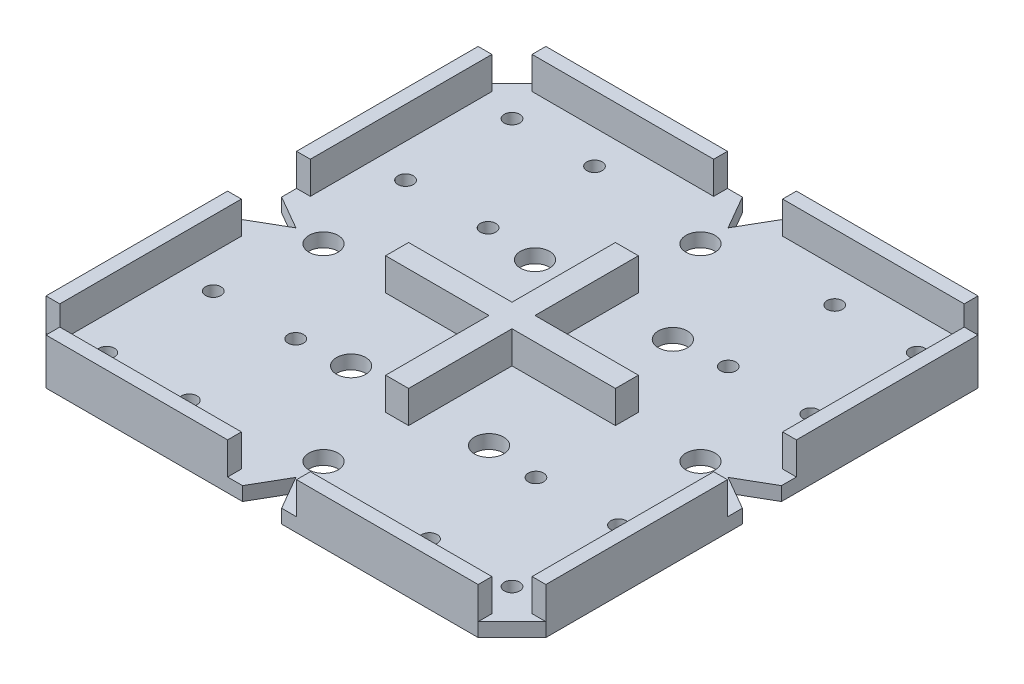
SolidWorks part; units mm, degrees
ref_plane "Front Plane" through (0, 0, 0) normal (0, 0, 1) x (1, 0, 0)
ref_plane "Top Plane" through (0, 0, 0) normal (0, 1, 0) x (1, 0, 0)
ref_plane "Right Plane" through (0, 0, 0) normal (1, 0, 0) x (0, 0, -1)
sketch "Sketch1" plane through (0, 0, 0) normal (0, 1, 0) x (1, 0, 0)
  line L1 (0, 0) -> (120, 0)
  line L2 (0, 0) -> (0, 120)
  line L3 (0, 120) -> (120, 120)
  line L4 (120, 0) -> (120, 120)
  dimension "D1" = 120
extrude "Boss-Extrude1" add sketch "Sketch1" along normal blind 3
sketch "Sketch3" plane through (0, 3, 0) normal (0, 1, 0) x (1, 0, 0)
  line L0 (0, 0) -> (120, 0) construction
  line L1 (0, 120) -> (0, 0) construction
  line L2 (0, 60) -> (120, 60) construction
  line L3 (120, 0) -> (120, 120) construction
  line L4 (60, 0) -> (60, 120) construction
  line L5 (120, 120) -> (0, 120) construction
  circle A0 centre (15.92, 15.92) radius 1.675
  circle A1 centre (33.87, 15.92) radius 1.675
  circle A2 centre (15.92, 39.08) radius 1.675
  circle A3 centre (33.87, 39.08) radius 1.675
  circle A4 centre (33.87, 80.92) radius 1.675
  circle A5 centre (15.92, 80.92) radius 1.675
  circle A6 centre (33.87, 104.08) radius 1.675
  circle A7 centre (15.92, 104.08) radius 1.675
  circle A8 centre (86.13, 39.08) radius 1.675
  circle A9 centre (104.08, 39.08) radius 1.675
  circle A10 centre (86.13, 15.92) radius 1.675
  circle A11 centre (104.08, 15.92) radius 1.675
  circle A12 centre (104.08, 104.08) radius 1.675
  circle A13 centre (86.13, 104.08) radius 1.675
  circle A14 centre (104.08, 80.92) radius 1.675
  circle A15 centre (86.13, 80.92) radius 1.675
  dimension "D5" = 3.35
  dimension "D1" = 15.92
  dimension "D2" = 15.92
  dimension "D3" = 17.95
  dimension "D4" = 23.16
extrude "Cut-Extrude2" cut sketch "Sketch3" against normal through all
sketch "Sketch4" plane through (0, 3, 0) normal (0, 1, 0) x (1, 0, 0)
  line L0 (52.5, 120) -> (60, 107.0096)
  line L1 (120, 120) -> (0, 120) construction
  line L2 (60, 107.0096) -> (67.5, 120)
  line L3 (67.5, 120) -> (52.5, 120)
  line L4 (0, 67.5) -> (12.9904, 60)
  line L5 (0, 120) -> (0, 0) construction
  line L6 (12.9904, 60) -> (0, 52.5)
  line L7 (0, 52.5) -> (0, 67.5)
  line L8 (120, 67.5) -> (107.0096, 60)
  line L9 (120, 0) -> (120, 120) construction
  line L10 (107.0096, 60) -> (120, 52.5)
  line L11 (120, 52.5) -> (120, 67.5)
  line L12 (67.5, 0) -> (60, 12.9904)
  line L13 (0, 0) -> (120, 0) construction
  line L14 (60, 12.9904) -> (52.5, 0)
  line L15 (52.5, 0) -> (67.5, 0)
  line L16 (0, 52.5) -> (0, 0) construction
  line L17 (0, 67.5) -> (0, 120) construction
  line L18 (52.5, 120) -> (0, 120) construction
  line L19 (67.5, 120) -> (120, 120) construction
  line L20 (120, 67.5) -> (120, 120) construction
  line L21 (120, 52.5) -> (120, 0) construction
  line L22 (120, 0) -> (67.5, 0) construction
  line L23 (52.5, 0) -> (0, 0) construction
  dimension "D1" = 15
  dimension "D2" = 15
extrude "Cut-Extrude3" cut sketch "Sketch4" against normal through all
sketch "Sketch5" plane through (0, 3, 0) normal (0, 1, 0) x (1, 0, 0)
  line L0 (60, 12.9904) -> (60, 107.0096) construction
  line L1 (12.9904, 60) -> (107.0096, 60) construction
  circle A0 centre (75, 40) radius 3.175
  circle A1 centre (45, 40) radius 3.175
  circle A2 centre (45, 80) radius 3.175
  circle A3 centre (75, 80) radius 3.175
  circle A8 centre (101.0096, 60) radius 3.175
  circle A9 centre (60, 18.9904) radius 3.175
  circle A10 centre (60, 101.0096) radius 3.175
  circle A11 centre (18.9904, 60) radius 3.175
  point P28 (0, 0)
  dimension "D3" = 6.35
  dimension "D1" = 20
  dimension "D2" = 15
  dimension "D4" = 6
  dimension "D5" = 6
  dimension "D6" = 6
  dimension "D7" = 6
extrude "Cut-Extrude4" cut sketch "Sketch5" against normal up to surface (3 mm away) up to face at (60, 0, -60)
sketch "Sketch8" plane through (0, 3, 0) normal (0, 1, 0) x (1, 0, 0)
  line L0 (60, 107.0096) -> (60, 85) construction
  line L1 (60, 12.9904) -> (60, 35) construction
  line L2 (12.9904, 60) -> (35, 60) construction
  line L3 (62.5, 85) -> (57.5, 85)
  line L4 (62.5, 85) -> (62.5, 35)
  line L5 (62.5, 35) -> (57.5, 35)
  line L6 (57.5, 85) -> (57.5, 35)
  line L7 (107.0096, 60) -> (85, 60) construction
  line L8 (104.08, 105.755) -> (87.805, 105.755) construction
  line L9 (85, 62.5) -> (35, 62.5)
  line L10 (85, 62.5) -> (85, 57.5)
  line L11 (85, 57.5) -> (35, 57.5)
  line L12 (35, 62.5) -> (35, 57.5)
  line L13 (107.0096, 114.3775) -> (67.5, 114.3775)
  line L14 (107.0096, 114.3775) -> (107.0096, 111.3775)
  line L15 (107.0096, 111.3775) -> (67.5, 111.3775)
  line L16 (67.5, 114.3775) -> (67.5, 111.3775)
  line L17 (107.0096, 105.755) -> (107.0096, 111.3775) construction
  line L18 (107.0096, 114.3775) -> (107.0096, 120) construction
  line L19 (120, 120) -> (67.5, 120) construction
  line L20 (105.755, 104.3139) -> (105.755, 72.5955) construction
  line L21 (111.3775, 107.0096) -> (105.755, 107.0096) construction
  line L22 (114.3775, 107.0096) -> (111.3775, 107.0096)
  line L23 (114.3775, 107.0096) -> (114.3775, 67.5)
  line L24 (114.3775, 67.5) -> (111.3775, 67.5)
  line L25 (111.3775, 107.0096) -> (111.3775, 67.5)
  line L26 (114.3775, 107.0096) -> (120, 107.0096) construction
  line L27 (120, 67.5) -> (120, 120) construction
  line L28 (114.3775, 52.5) -> (111.3775, 52.5)
  line L29 (111.3775, 12.9904) -> (111.3775, 52.5)
  line L30 (114.3775, 12.9904) -> (111.3775, 12.9904)
  line L31 (114.3775, 12.9904) -> (114.3775, 52.5)
  line L32 (107.0096, 8.6225) -> (67.5, 8.6225)
  line L33 (67.5, 5.6225) -> (67.5, 8.6225)
  line L34 (107.0096, 5.6225) -> (67.5, 5.6225)
  line L35 (107.0096, 5.6225) -> (107.0096, 8.6225)
  line L36 (12.9904, 5.6225) -> (12.9904, 8.6225)
  line L37 (12.9904, 5.6225) -> (52.5, 5.6225)
  line L38 (52.5, 5.6225) -> (52.5, 8.6225)
  line L39 (12.9904, 8.6225) -> (52.5, 8.6225)
  line L40 (5.6225, 12.9904) -> (5.6225, 52.5)
  line L41 (5.6225, 12.9904) -> (8.6225, 12.9904)
  line L42 (8.6225, 12.9904) -> (8.6225, 52.5)
  line L43 (5.6225, 52.5) -> (8.6225, 52.5)
  line L44 (5.6225, 67.5) -> (8.6225, 67.5)
  line L45 (8.6225, 107.0096) -> (8.6225, 67.5)
  line L46 (5.6225, 107.0096) -> (8.6225, 107.0096)
  line L47 (5.6225, 107.0096) -> (5.6225, 67.5)
  line L48 (12.9904, 111.3775) -> (52.5, 111.3775)
  line L49 (52.5, 114.3775) -> (52.5, 111.3775)
  line L50 (12.9904, 114.3775) -> (52.5, 114.3775)
  line L51 (12.9904, 114.3775) -> (12.9904, 111.3775)
  circle A2 centre (104.08, 104.08) radius 1.675 construction
  point P20 (60, 85)
  point P21 (60, 35)
  point P26 (35, 60)
  point P48 (110.3775, 69.8114)
  dimension "D1" = 5
  dimension "D2" = 50
  dimension "D3" = 5
  dimension "D4" = 50
  dimension "D5" = 3
extrude "Boss-Extrude5" add sketch "Sketch8" along normal blind 7 contours L9 L12 L11 L6 | L11 L10 L9 L4 | L31 L28 L29 L30 | L34 L33 L32 L35 | L39 L38 L37 L36 | L42 L43 L40 L41 | L47 L44 L45 L46 | L50 L49 L48 L51 | L13 L16 L15 L14 | L23 L24 L25 L22
sketch "Sketch9" plane through (0, 3, 0) normal (0, 1, 0) x (1, 0, 0)
  line L4 (120, 120) -> (120, 0)
  line L5 (120, 0) -> (0, 0)
  line L6 (0, 0) -> (0, 120)
  line L7 (0, 120) -> (120, 120)
  line L16 (107.0096, 114.3775) -> (12.9904, 114.3775)
  line L17 (12.9904, 114.3775) -> (5.6225, 107.0096)
  line L18 (5.6225, 107.0096) -> (5.6225, 12.9904)
  line L19 (5.6225, 12.9904) -> (12.9904, 5.6225)
  line L20 (12.9904, 5.6225) -> (107.0096, 5.6225)
  line L21 (107.0096, 5.6225) -> (114.3775, 12.9904)
  line L22 (114.3775, 12.9904) -> (114.3775, 107.0096)
  line L23 (114.3775, 107.0096) -> (114.3775, 67.5) construction
  line L24 (114.3775, 107.0096) -> (107.0096, 114.3775)
extrude "Cut-Extrude5" cut sketch "Sketch9" against normal through all
